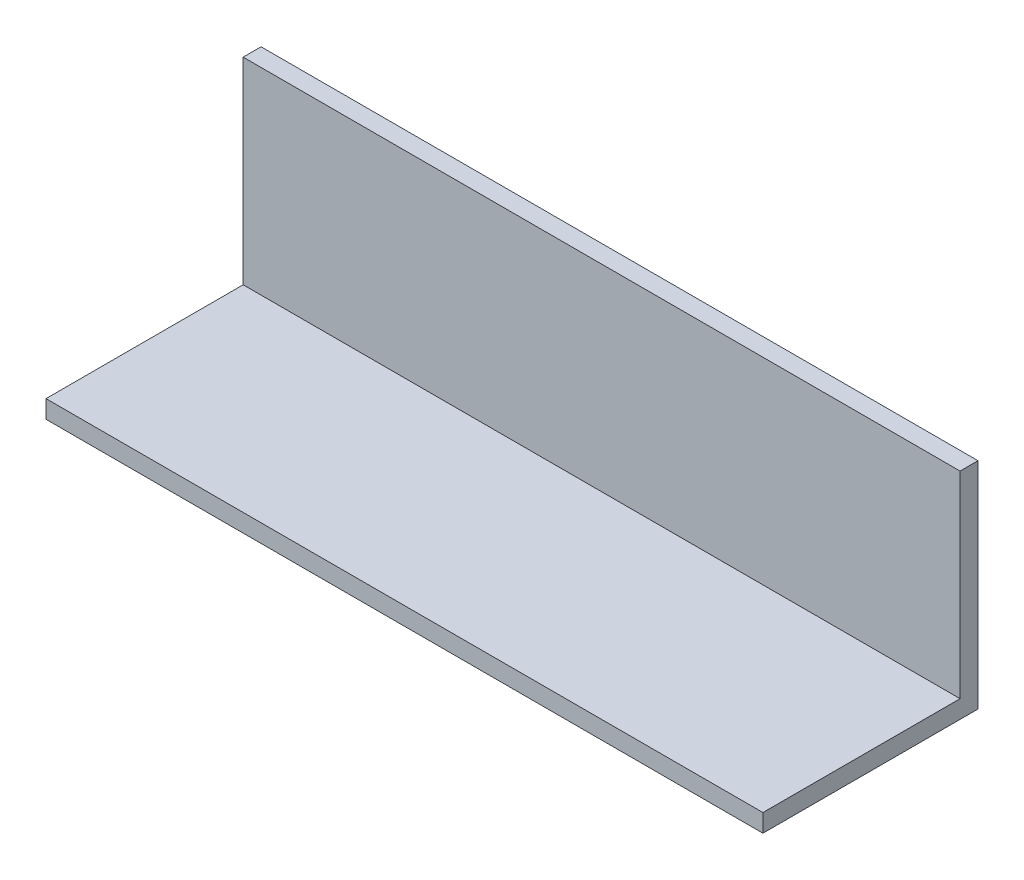
SolidWorks part; units mm, degrees
ref_plane "Front" through (0, 0, 0) normal (0, 0, 1) x (1, 0, 0)
ref_plane "Top" through (0, 0, 0) normal (0, 1, 0) x (1, 0, 0)
ref_plane "Right" through (0, 0, 0) normal (1, 0, 0) x (0, 0, -1)
sketch "Sketch1" plane through (0, 0, 0) normal (0, 0, 1) x (1, 0, 0)
  line L1 (-1.846, 0.7117) -> (125.154, 0.7117)
  line L2 (-1.846, 0.7117) -> (-1.846, -37.3883)
  line L3 (-1.846, -37.3883) -> (125.154, -37.3883)
  line L4 (125.154, 0.7117) -> (125.154, -37.3883)
  dimension "D1" = 38.1
  dimension "D2" = 127
extrude "Boss-Extrude1" add sketch "Sketch1" along normal blind 38.1
sketch "Sketch2" plane through (0, 0, 38.1) normal (0, 0, 1) x (1, 0, 0)
  line L0 (125.154, -37.3883) -> (125.154, 0.7117) construction
  line L1 (-1.846, 0.7117) -> (125.154, 0.7117)
  line L2 (-1.846, 0.7117) -> (-1.846, -34.2133)
  line L3 (-1.846, -34.2133) -> (125.154, -34.2133)
  line L4 (125.154, 0.7117) -> (125.154, -34.2133)
  dimension "D1" = 34.925
extrude "Cut-Extrude1" cut sketch "Sketch2" against normal blind 34.925
